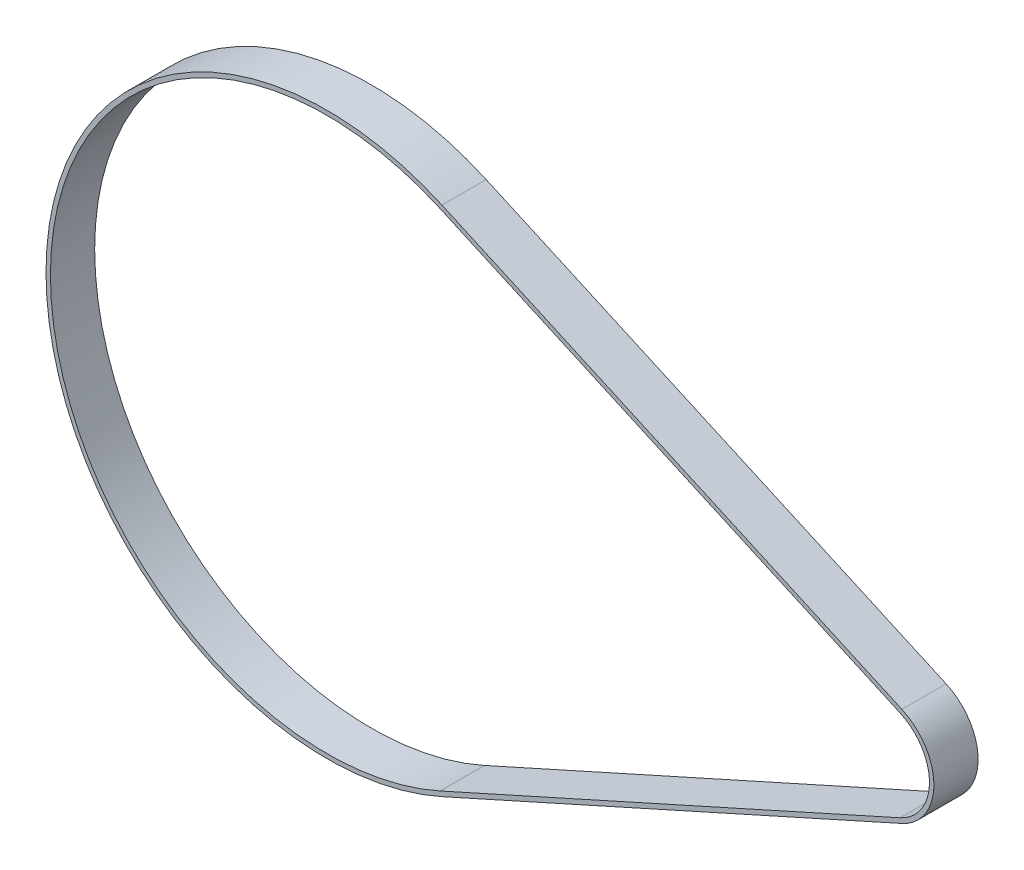
SolidWorks part; units mm, degrees
ref_plane "Front Plane" through (0, 0, 0) normal (0, 0, 1) x (1, 0, 0)
ref_plane "Top Plane" through (0, 0, 0) normal (0, 1, 0) x (1, 0, 0)
ref_plane "Right Plane" through (0, 0, 0) normal (1, 0, 0) x (0, 0, -1)
sketch "Sketch2" plane through (0, 0, 0) normal (0, 0, 1) x (1, 0, 0)
  line L0 (0, 0) -> (1, 0) construction
  line L1 (0, 0) -> (0, 1) construction
  line L2 (51.25, 114.0107) -> (259.225, 20.5219)
  line L3 (259.225, -20.5219) -> (51.25, -114.0107)
  arc A0 (51.25, -114.0107) -> (51.25, 114.0107) centre (0, 0) cw
  arc A1 (259.225, 20.5219) -> (259.225, -20.5219) centre (250, 0) cw
extrude "Extrude-Thin1" add sketch "Sketch2" along normal mid plane 20 thin thin type one direction wall 2
